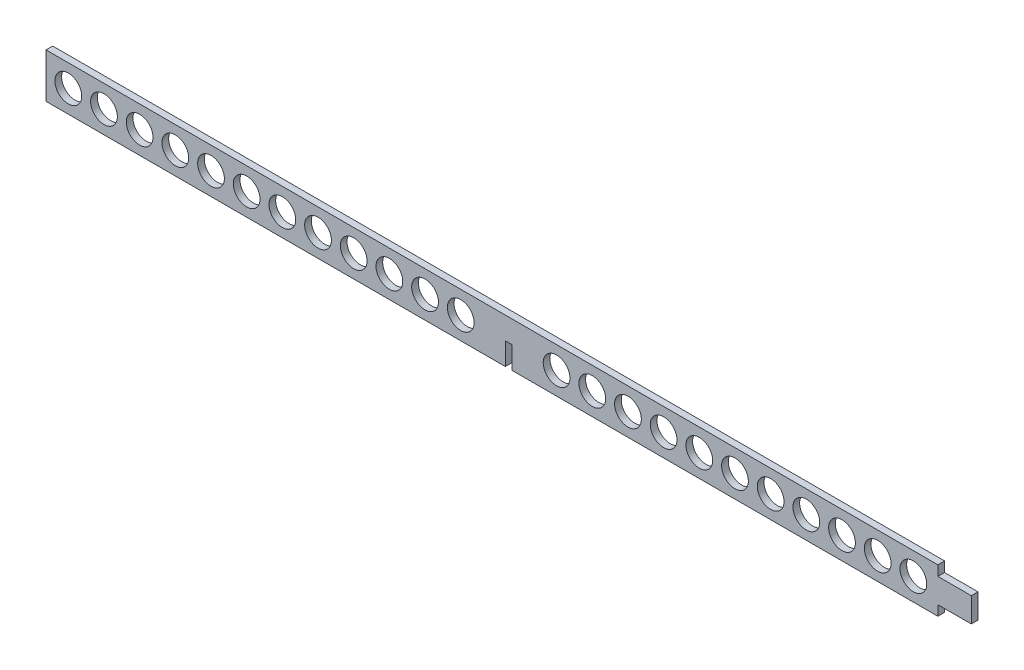
SolidWorks part; units mm, degrees
material "Pine"
ref_plane "Front Plane" through (0, 0, 0) normal (0, 0, 1) x (1, 0, 0)
ref_plane "Top Plane" through (0, 0, 0) normal (0, 1, 0) x (1, 0, 0)
ref_plane "Right Plane" through (0, 0, 0) normal (1, 0, 0) x (0, 0, -1)
sketch "Sketch1" plane through (0, 0, 0) normal (0, 0, 1) x (1, 0, 0)
  line L1 (0, 0) -> (-415, 0)
  line L2 (0, 0) -> (0, 20)
  line L3 (0, 20) -> (-415, 20)
  line L4 (-415, 0) -> (-415, 20)
  dimension "D1" = 20
  dimension "D2" = 415
extrude "Boss-Extrude1" add sketch "Sketch1" along normal blind 3
sketch "Sketch2" plane through (0, 0, 3) normal (0, 0, 1) x (1, 0, 0)
  line L0 (0, 10) -> (-415, 10) construction
  line L1 (0, 0) -> (0, 20) construction
  line L2 (-415, 20) -> (-415, 0) construction
  line L8 (-207.5, 20) -> (-207.5, 0) construction
  line L9 (-415, 0) -> (0, 0) construction
  line L10 (0, 4.5) -> (0, 15.5) construction
  line L13 (0, 20) -> (-15, 20)
  line L14 (0, 4.5) -> (-15, 4.5)
  line L15 (0, 4.5) -> (0, 0)
  line L16 (0, 0) -> (-15, 0)
  line L17 (-15, 4.5) -> (-15, 0)
  line L18 (-15, 15.5) -> (-15, 20)
  line L19 (0, 15.5) -> (-15, 15.5)
  line L20 (0, 15.5) -> (0, 20)
  line L21 (0, 20) -> (-415, 20) construction
  line L23 (-209, 10) -> (-206, 10)
  line L24 (-209, 10) -> (-209, 0)
  line L25 (-209, 0) -> (-206, 0)
  line L26 (-206, 10) -> (-206, 0)
  circle A3 centre (-405, 10) radius 6
  circle A4 centre (-389, 10) radius 6
  circle A5 centre (-373, 10) radius 6
  circle A6 centre (-357, 10) radius 6
  circle A7 centre (-341, 10) radius 6
  circle A8 centre (-325, 10) radius 6
  circle A9 centre (-309, 10) radius 6
  circle A10 centre (-293, 10) radius 6
  circle A11 centre (-277, 10) radius 6
  circle A12 centre (-261, 10) radius 6
  circle A13 centre (-245, 10) radius 6
  circle A14 centre (-229, 10) radius 6
  circle A16 centre (-26, 10) radius 6
  circle A17 centre (-42, 10) radius 6
  circle A18 centre (-58, 10) radius 6
  circle A19 centre (-74, 10) radius 6
  circle A20 centre (-90, 10) radius 6
  circle A21 centre (-106, 10) radius 6
  circle A22 centre (-122, 10) radius 6
  circle A23 centre (-138, 10) radius 6
  circle A24 centre (-154, 10) radius 6
  circle A25 centre (-170, 10) radius 6
  circle A26 centre (-186, 10) radius 6
  point P12 (-207.5, 0)
  point P67 (0, 10)
  dimension "D2" = 12
  dimension "D3" = 10
  dimension "D1" = 3
  dimension "D5" = 16
  dimension "D6" = 11
  dimension "D7" = 15
  dimension "D4" = 12
extrude "Cut-Extrude1" cut sketch "Sketch2" against normal through all both and the other way through all
